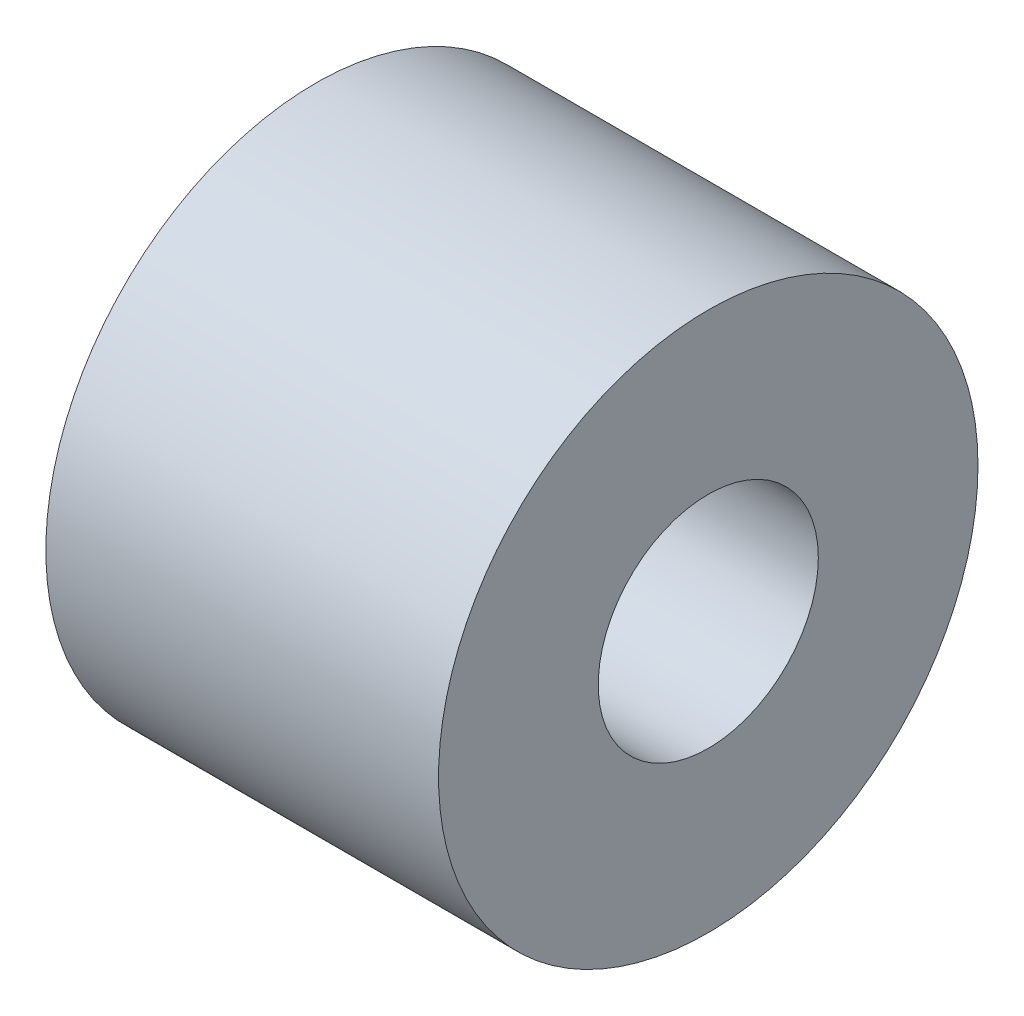
SolidWorks part; units mm, degrees
ref_plane "Front" through (0, 0, 0) normal (0, 0, 1) x (1, 0, 0)
ref_plane "Top" through (0, 0, 0) normal (0, 1, 0) x (1, 0, 0)
ref_plane "Right" through (0, 0, 0) normal (1, 0, 0) x (0, 0, -1)
sketch "Sketch1" plane through (0, 0, 0) normal (1, 0, 0) x (0, 0, -1)
  circle A0 centre (0, 0) radius 2.55
  circle A1 centre (0, 0) radius 6.25
  dimension "D1" = 5.1
  dimension "D2" = 12.5
extrude "Boss-Extrude1" add sketch "Sketch1" along normal mid plane 9.1
